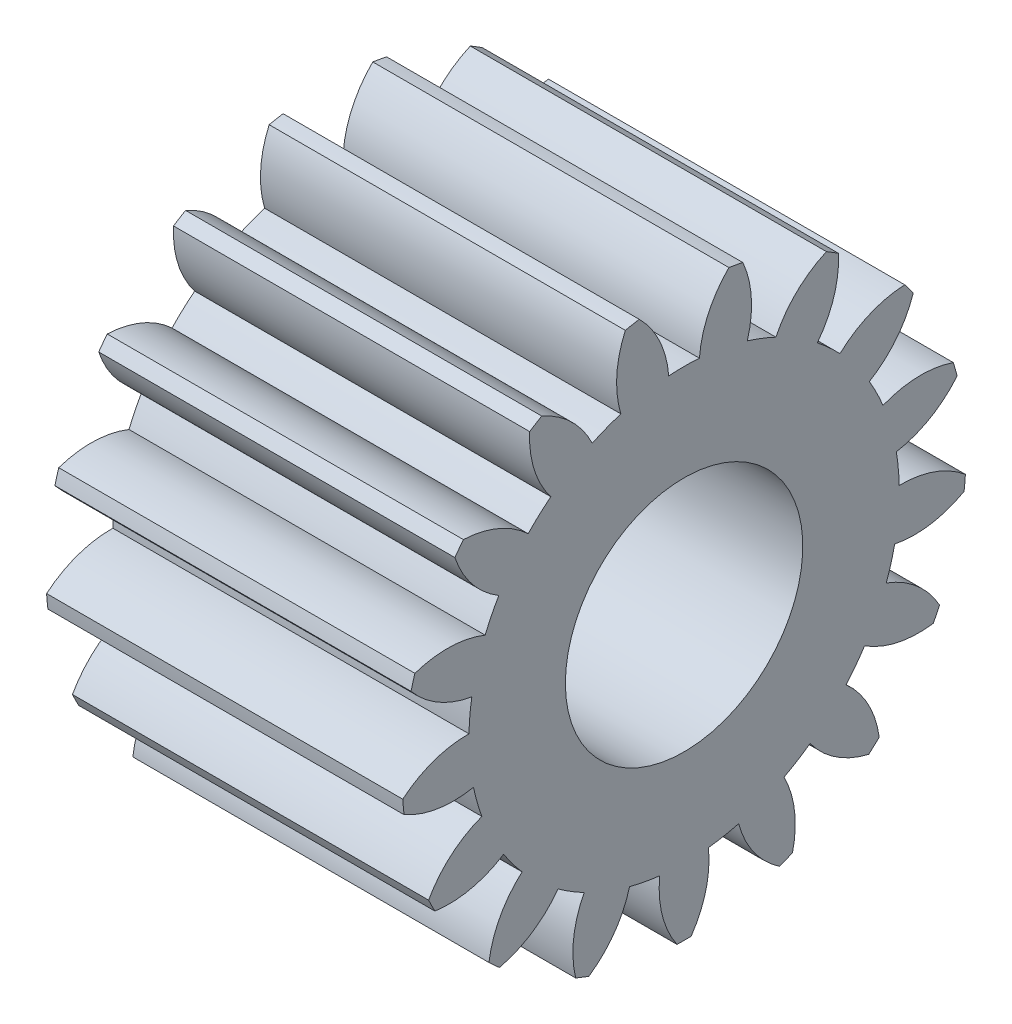
SolidWorks part; units mm, degrees
ref_plane "Plane1" through (0, 0, 0) normal (0, 0, 1) x (1, 0, 0)
ref_plane "Plane2" through (0, 0, 0) normal (0, 1, 0) x (1, 0, 0)
ref_plane "Plane3" through (0, 0, 0) normal (1, 0, 0) x (0, 0, -1)
other "Configuration Table"
sketch "HoldingSke" plane through (0, 0, 0) normal (0, 1, 0) x (1, 0, 0)
  line L0 (0, 0) -> (0.9563, -0.2924)
  line L1 (-15, 0) -> (100, 0) construction
  line L2 (0, 0) -> (-2.1039, 2.3779)
  line L3 (0, 0) -> (-11.863, 4.5341)
  line L4 (0, 0) -> (8.2586, 2.5249)
  line L5 (0, 0) -> (-46.8476, -17.4728)
  line L6 (0, 0) -> (-9.9476, -6.7116)
  line L7 (-2.1039, 2.3779) -> (8.6586, 51.2059)
  line L8 (-76.2, 54.61) -> (-74.8, 54.61)
  line L9 (-71.009, 38.7566) -> (-53.1078, 45.2721)
  line L10 (-76.2, 71.12) -> (104.1128, 71.12)
  line L11 (0, 0) -> (-12, 0)
  line L12 (-76.2, 101.6) -> (-76.162, 101.6)
  line L13 (24.9733, 27.94) -> (52.9518, 28.4284)
  line L14 (24.9733, 27.94) -> (24.9743, 27.94)
  line L15 (24.9733, 27.94) -> (100.4006, 29.5858)
  line L16 (-63.627, -1) -> (-12.827, -1)
  circle A0 centre (0, 0) radius 4
  circle A1 centre (0, 0) radius 7.249
  circle A2 centre (0, 0) radius 37.5
  circle A3 centre (0, 0) radius 4
  dimension "MHD" = 14.498
  dimension "Hub_dia" = 75
  dimension "Bore" = 8
  dimension "MBD" = 8
  dimension "Num_teeth" = 17
  dimension "Pitch" = 1
  dimension "Overall_len" = 50
  dimension "Show_teeth" = 17
  dimension "Thickness" = 12
  dimension "OAL" = 50.0001
  dimension "T_dim" = 1.4
  dimension "Ap" = 20
  dimension "H" = 19.05
  dimension "Pitch_radius" = 180.3128
  dimension "Width" = 12
  dimension "Backlash" = 0.038
  dimension "Addendum_fac" = 1
  dimension "Dedendum_fac" = 1.25
  dimension "Clearance_fac" = 0.25
  dimension "Dedendum_add" = 0.001
  dimension "Module" = 1
sketch "BasProSke" plane through (0, 0, 0) normal (0, 1, 0) x (1, 0, 0)
  line L0 (-10, 0) -> (60, 0) construction
  line L1 (0, 0) -> (0, 9.5)
  line L2 (0, 0) -> (12, 0)
  line L3 (12, 0) -> (12, 9.5)
  line L4 (12, 9.5) -> (0, 9.5)
  dimension "Thickness" = 12
  dimension "Diameter" = 19
revolve "Base-Revolve" add sketch "BasProSke" angle 360 about L0
sketch "TooCutSke" plane through (0, 0, 0) normal (1, 0, 0) x (0, 0, -1)
  line L1 (0, 0) -> (0, 107) construction
  line L2 (0, 0) -> (-0.8507, 8.4573) construction
  line L3 (0, 0) -> (-3.1126, 16.6509) construction
  line L4 (-0.8507, 8.4573) -> (-1.5563, 8.3254) construction
  arc A0 (0.5169, 7.2306) -> (-0.5169, 7.2306) centre (0, 0) ccw
  arc A1 (1.5331, 9.4012) -> (-1.5331, 9.4012) centre (0, 0) ccw
  circle A2 centre (0, 0) radius 8.5 construction
  circle A3 centre (0, 0) radius 7.9874 construction
  arc A4 (-0.5169, 7.2306) -> (-1.5331, 9.4012) centre (-3.9066, 6.9668) ccw
  arc A5 (1.5331, 9.4012) -> (0.5169, 7.2306) centre (3.9066, 6.9668) ccw
  dimension "Root_dia" = 14.498
  dimension "Overcut_dia" = 19.0508
  dimension "Pitch_dia" = 17
  dimension "Base_dia" = 15.9748
  dimension "Flank_rad" = 3.4
  dimension "Half_ang" = 10.588
  dimension "Half_CT" = 0.7178
extrude "ToothCut" cut sketch "TooCutSke" along normal through all
fillet "Breaks" [suppressed] radius 0.02
fillet "RootFillets" [suppressed] radius 0.251
pattern_circular "TeethCuts" count 17 every 21.176 about axis through (-10, 0, 0) along (1, 0, 0) of "ToothCut", "RootFillets", "Breaks"
sketch "HubNeaOneSke" plane through (0, 0, 0) normal (-1, 0, 0) x (0, 0, 1)
  circle A0 centre (0, 0) radius 7.249
  dimension "Diameter" = 14.498
extrude "HubNearOne" [suppressed] add sketch "HubNeaOneSke" along normal blind 38.0001
sketch "HubNeaBotSke" plane through (0, 0, 0) normal (-1, 0, 0) x (0, 0, 1)
  circle A0 centre (0, 0) radius 7.249
  dimension "Diameter" = 14.498
extrude "HubNearBoth" [suppressed] add sketch "HubNeaBotSke" along normal blind 19
ref_plane "FarPln" through (12, 0, 0) normal (1, 0, 0) x (0, 0, -1)
sketch "HubFarSke" plane through (12, 0, 0) normal (1, 0, 0) x (0, 0, -1)
  circle A0 centre (0, 0) radius 7.249
  dimension "Diameter" = 14.498
extrude "HubFar" [suppressed] add sketch "HubFarSke" along normal blind 19
sketch "BorSke" plane through (0, 0, 0) normal (1, 0, 0) x (0, 0, -1)
  circle A0 centre (0, 0) radius 4
  dimension "Diameter" = 8
extrude "Bore" cut sketch "BorSke" along normal mid plane 100.0001
sketch "KeySke" plane through (0, 0, 0) normal (1, 0, 0) x (0, 0, -1)
  line L0 (-1.5, 0) -> (-1.5, 5.4)
  line L1 (-1.5, 5.4) -> (1.5, 5.4)
  line L2 (1.5, 5.4) -> (1.5, 0)
  line L3 (0, 0) -> (0, 34) construction
  line L4 (-1.5, 0) -> (1.5, 0)
  dimension "Offset" = 5.4
  dimension "Width" = 3
extrude "Keyway" [suppressed] cut sketch "KeySke" along normal mid plane 100.0001
pattern_circular "Keyway2" [suppressed] count 2 every 90 about axis through (-10, 0, 0) along (1, 0, 0)
equation "' \"Module@HoldingSke\" = 6.35"
equation "' \"Num_teeth@HoldingSke\" = 12"
equation "' \"Ap@HoldingSke\" =  20"
equation "' \"Ap@HoldingSke\" = 20"
equation "' \"Width@HoldingSke\" = 0.5 * 25.4"
equation "' \"Hub_dia@HoldingSke\"= 1 * 25.4"
equation "' \"Hub_dia@HoldingSke\" = 1 * 25.4"
equation "' \"Overall_len@HoldingSke\" = 1.0 * 25.4"
equation "' \"Bore@HoldingSke\" = 0.75 * 25.4"
equation "' \"T_dim@HoldingSke\" = 0.1 * 25.4"
equation "' \"Width@KeySke\" = 0.25 * 25.4"
equation "' \"Show_teeth@HoldingSke\" = 13"
equation "' \"Backlash@HoldingSke\" = 0.009 * 25.4"
equation "' \"Addendum_fac@HoldingSke\" = 1.0"
equation "' \"Dedendum_fac@HoldingSke\" = 1.25"
equation "' \"Dedendum_add@HoldingSke\" = 0.00005 * 25.4"
equation "' \"Clearance_fac@HoldingSke\" = 0.25"
equation "\"Pitch@HoldingSke\" = 1 / \"Module@HoldingSke\""
equation "\"Overcut_dia@TooCutSke\" = (\"Num_teeth@HoldingSke\" + 2 * \"Addendum_fac@HoldingSke\") / \"Pitch@HoldingSke\" + 0.002 * 25.4"
equation "\"Pitch_dia@TooCutSke\" = \"Num_teeth@HoldingSke\" / \"Pitch@HoldingSke\""
equation "\"Base_dia@TooCutSke\" = \"Num_teeth@HoldingSke\" / \"Pitch@HoldingSke\" * cos((\"Ap@HoldingSke\"  * 3.14159265 / 180))"
equation "\"Root_dia@TooCutSke\" = (\"Num_teeth@HoldingSke\" + 2) / \"Pitch@HoldingSke\" - 2 * (\"Addendum_fac@HoldingSke\" + \"Dedendum_fac@HoldingSke\") / \"Pitch@HoldingSke\" - \"Dedendum_add@HoldingSke\" * 2"
equation "\"Half_ang@TooCutSke\" = 180 / \"Num_teeth@HoldingSke\""
equation "\"Half_CT@TooCutSke\" = \"Num_teeth@HoldingSke\" / \"Pitch@HoldingSke\" * sin((3.14159265 / 2 / \"Num_teeth@HoldingSke\")) / 2 - 7 * \"Backlash@HoldingSke\" / 4"
equation "\"Flank_rad@TooCutSke\" = \"Num_teeth@HoldingSke\" / \"Pitch@HoldingSke\" / 5"
equation "\"Radius@RootFillets\" = \"Clearance_fac@HoldingSke\" / \"Pitch@HoldingSke\" + \"Dedendum_add@HoldingSke\""
equation "\"Break_rad@Breaks\" = 0.02 / \"Pitch@HoldingSke\""
equation "\"Thickness@HoldingSke\" = \"Width@HoldingSke\""
equation "\"OAL@HoldingSke\" = \"Thickness@HoldingSke\""
equation "\"MHD@HoldingSke\" = (\"Num_teeth@HoldingSke\" + 2) / \"Pitch@HoldingSke\" - 2 * (\"Addendum_fac@HoldingSke\" + \"Dedendum_fac@HoldingSke\")  / \"Pitch@HoldingSke\" - \"Dedendum_add@HoldingSke\" * 2"
equation "\"MBD@HoldingSke\" = (\"Num_teeth@HoldingSke\" + 2) / \"Pitch@HoldingSke\" - 2 * (\"Addendum_fac@HoldingSke\" + \"Dedendum_fac@HoldingSke\")  / \"Pitch@HoldingSke\" - \"Dedendum_add@HoldingSke\" * 2 - 0.002 * 25.4"
equation "\"MHD@HoldingSke\" = ((sgn( \"MHD@HoldingSke\" - \"Hub_dia@HoldingSke\" )-1)*( \"MHD@HoldingSke\" - \"Hub_dia@HoldingSke\" ))/-2+ \"Hub_dia@HoldingSke\""
equation "\"MBD@HoldingSke\" = ((sgn( \"MBD@HoldingSke\" - \"Bore@HoldingSke\" )-1)*( \"MBD@HoldingSke\" - \"Bore@HoldingSke\" ))/-2+ \"Bore@HoldingSke\""
equation "\"OAL@HoldingSke\" = ((sgn( \"OAL@HoldingSke\" - \"Overall_len@HoldingSke\" )+1)*( \"OAL@HoldingSke\" - \"Overall_len@HoldingSke\" ))/2 + \"Overall_len@HoldingSke\" + 0.000002 * 25.4"
equation "\"Num_teeth@TeethCuts\" = int( \"Show_teeth@HoldingSke\" ) + 1"
equation "\"Num_teeth@TeethCuts\" = ((sgn( \"Num_teeth@TeethCuts\" - \"Num_teeth@HoldingSke\" )-1)*( \"Num_teeth@TeethCuts\" - \"Num_teeth@HoldingSke\" ))/-2+ \"Num_teeth@HoldingSke\""
equation "\"Num_teeth@TeethCuts\" = ((sgn( \"Num_teeth@TeethCuts\" - 2.0)+1)*( \"Num_teeth@TeethCuts\" - 2.0))/2 +2.0"
equation "\"Angle@TeethCuts\" = 360.0 / \"Num_teeth@HoldingSke\""
equation "\"Diameter@BasProSke\" = (\"Num_teeth@HoldingSke\" + 2 * \"Addendum_fac@HoldingSke\") / \"Pitch@HoldingSke\""
equation "\"Thickness@BasProSke\"  = \"Thickness@HoldingSke\""
equation "' \"Fillet_rad@BasProSke\" =  \"Thickness@HoldingSke\" * 0.05"
equation "' \"Fillet_rad@BasProSke\" = \"Thickness@HoldingSke\" * 0.05"
equation "\"MHD@HoldingSke\" = ((sgn( \"MHD@HoldingSke\" - \"Root_dia@TooCutSke\" )-1)*( \"MHD@HoldingSke\" - \"Root_dia@TooCutSke\" ))/-2+ \"Root_dia@TooCutSke\""
equation "\"Diameter@HubNeaOneSke\" = \"MHD@HoldingSke\""
equation "\"Length@HubNearOne\" = \"OAL@HoldingSke\" - \"Thickness@BasProSke\""
equation "\"Diameter@HubNeaBotSke\" = \"MHD@HoldingSke\""
equation "\"Length@HubNearBoth\" = ( \"OAL@HoldingSke\" - \"Thickness@BasProSke\" ) / 2.0"
equation "\"Thickness@FarPln\" = \"Thickness@BasProSke\""
equation "\"Diameter@HubFarSke\" = \"MHD@HoldingSke\""
equation "\"Length@HubFar\" = ( \"OAL@HoldingSke\" - \"Thickness@BasProSke\" ) / 2.0"
equation "\"Diameter@BorSke\" = \"MBD@HoldingSke\""
equation "\"D1@Bore\" = \"OAL@HoldingSke\" * 2.0"
equation "\"D1@Keyway\" = \"OAL@HoldingSke\" * 2.0"
equation "\"Offset@KeySke\" = \"T_dim@HoldingSke\" + \"MBD@HoldingSke\" / 2.0"
